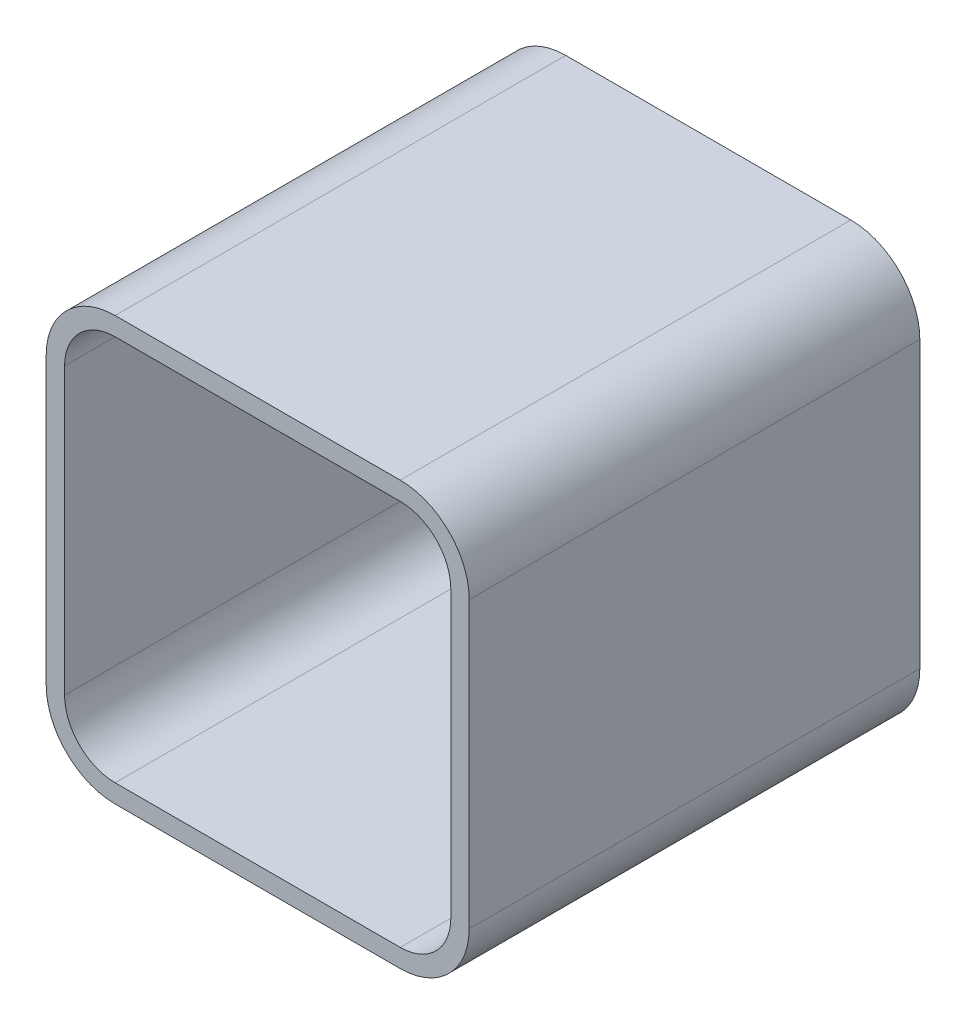
SolidWorks part; units mm, degrees
ref_plane "Front Plane" through (0, 0, 0) normal (0, 0, 1) x (1, 0, 0)
ref_plane "Top Plane" through (0, 0, 0) normal (0, 1, 0) x (1, 0, 0)
ref_plane "Right Plane" through (0, 0, 0) normal (1, 0, 0) x (0, 0, -1)
sketch "Sketch1" plane through (0, 0, 0) normal (0, 0, 1) x (1, 0, 0)
  line L1 (21, -21) -> (-21, -21)
  line L2 (21, -21) -> (21, 21)
  line L3 (21, 21) -> (-21, 21)
  line L4 (-21, -21) -> (-21, 21)
  line L5 (21, -21) -> (-21, 21) construction
  line L6 (21, 21) -> (-21, -21) construction
  point P0 (0, 0)
  dimension "D1" = 42
extrude "Boss-Extrude1" add sketch "Sketch1" along normal blind 2
fillet "Fillet1" radius 5.5 4 edges at (-21, -21, 1) (21, -21, 1) (-21, 21, 1) (21, 21, 1)
sketch "Sketch2" plane through (0, 0, 0) normal (0, 0, 1) x (1, 0, 0)
  line L8 (-23, 15.5) -> (-23, -15.5)
  line L9 (-15.5, -23) -> (15.5, -23)
  line L10 (23, -15.5) -> (23, 15.5)
  line L11 (15.5, 23) -> (-15.5, 23)
  line L12 (-23, 15.5) -> (-23, -15.5)
  line L13 (-15.5, -23) -> (15.5, -23)
  line L14 (23, -15.5) -> (23, 15.5)
  line L15 (15.5, 23) -> (-15.5, 23)
  line L16 (-21, 15.5) -> (-21, -15.5)
  line L17 (-15.5, -21) -> (15.5, -21)
  line L18 (21, -15.5) -> (21, 15.5)
  line L19 (15.5, 21) -> (-15.5, 21)
  line L20 (-21, 15.5) -> (-21, -15.5)
  line L21 (-15.5, -21) -> (15.5, -21)
  line L22 (21, -15.5) -> (21, 15.5)
  line L23 (15.5, 21) -> (-15.5, 21)
  arc A8 (-23, -15.5) -> (-15.5, -23) centre (-15.5, -15.5) ccw
  arc A9 (15.5, -23) -> (23, -15.5) centre (15.5, -15.5) ccw
  arc A10 (23, 15.5) -> (15.5, 23) centre (15.5, 15.5) ccw
  arc A11 (-15.5, 23) -> (-23, 15.5) centre (-15.5, 15.5) ccw
  arc A12 (-23, -15.5) -> (-15.5, -23) centre (-15.5, -15.5) ccw
  arc A13 (15.5, -23) -> (23, -15.5) centre (15.5, -15.5) ccw
  arc A14 (23, 15.5) -> (15.5, 23) centre (15.5, 15.5) ccw
  arc A15 (-15.5, 23) -> (-23, 15.5) centre (-15.5, 15.5) ccw
  arc A16 (-21, -15.5) -> (-15.5, -21) centre (-15.5, -15.5) ccw
  arc A17 (15.5, -21) -> (21, -15.5) centre (15.5, -15.5) ccw
  arc A18 (21, 15.5) -> (15.5, 21) centre (15.5, 15.5) ccw
  arc A19 (-15.5, 21) -> (-21, 15.5) centre (-15.5, 15.5) ccw
  arc A20 (-21, -15.5) -> (-15.5, -21) centre (-15.5, -15.5) ccw
  arc A21 (15.5, -21) -> (21, -15.5) centre (15.5, -15.5) ccw
  arc A22 (21, 15.5) -> (15.5, 21) centre (15.5, 15.5) ccw
  arc A23 (-15.5, 21) -> (-21, 15.5) centre (-15.5, 15.5) ccw
  dimension "D1" = 2
  dimension "D2" = 0
extrude "Boss-Extrude2" add sketch "Sketch2" along normal blind 49
